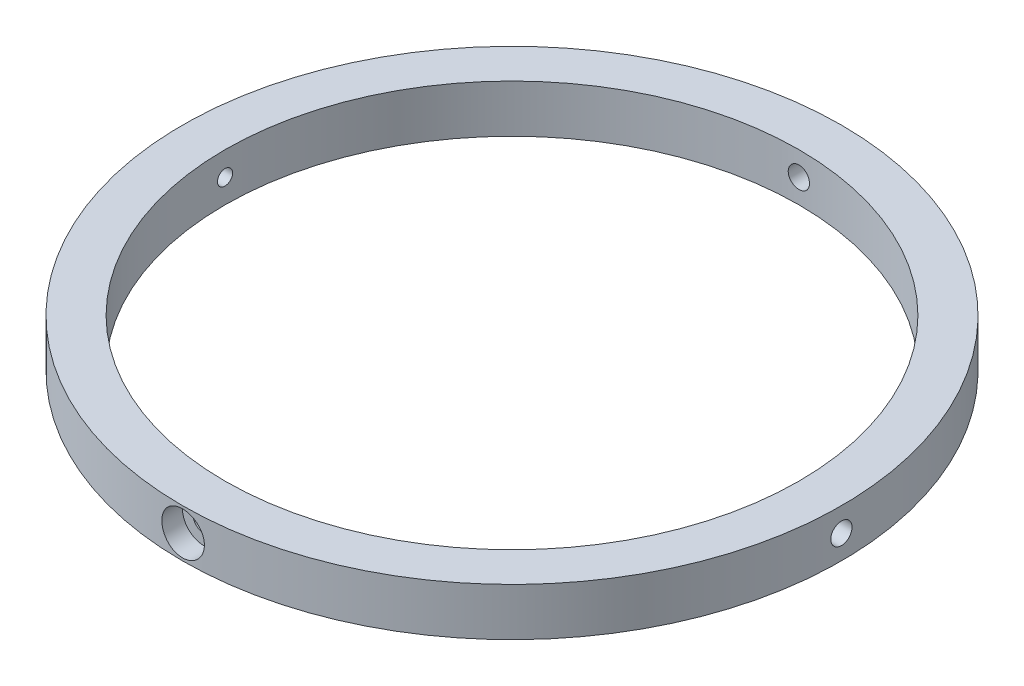
SolidWorks part; units mm, degrees
material "6061-T6 (SS)"
ref_plane "Front Plane" through (0, 0, 0) normal (0, 0, 1) x (1, 0, 0)
ref_plane "Top Plane" through (0, 0, 0) normal (0, 1, 0) x (1, 0, 0)
ref_plane "Right Plane" through (0, 0, 0) normal (1, 0, 0) x (0, 0, -1)
sketch "Sketch1" plane through (0, 0, 0) normal (0, 1, 0) x (1, 0, 0)
  circle A0 centre (0, 0) radius 49.2125
  circle A1 centre (0, 0) radius 42.8625
  dimension "D1" = 98.425
  dimension "D2" = 6.35
extrude "Boss-Extrude1" add sketch "Sketch1" along normal mid plane 7.1437
hole_wizard "Hole2" positions "3DSketch1" profile "Sketch3" legacy
sketch3d "3DSketch1"
  point P0 (49.2125, 0, 0)
  point P3 (0, 0, 0)
sketch "Sketch3" plane through (49.2125, 0, 0) normal (0, 1, 0) x (0, 0, -1)
  line L0 (0, 0) -> (0, 2.3813)
  line L1 (0, 2.3813) -> (1.5875, 2.3813)
  line L2 (1.5875, 2.3813) -> (1.5875, 0)
  line L3 (1.5875, 0) -> (0, 0)
  line L4 (0, 110) -> (0, -10) construction
  dimension "Diameter" = 3.175
  dimension "Depth" = 2.3813
hole_wizard "#4-40 Tapped Hole1" positions "Sketch6" profile "Sketch7" tap size "#4-40" standard "ANSI Inch"
sketch "Sketch6" plane through (46.8313, 0, 0) normal (1, 0, 0) x (0, 0, -1)
  point P0 (0, 0)
cosmetic thread "Hole Thread1" parameters "D1"=3.9899, "D2"=2.8448
sketch "Sketch7" plane through (46.8313, 0, 0) normal (0, 1, 0) x (0, 0, -1)
  line L0 (0, 0) -> (0, 9.5692)
  line L1 (0, 9.5692) -> (1.1303, 8.89)
  line L2 (1.1303, 8.89) -> (1.1303, 0)
  line L5 (1.1303, 0) -> (0, 0)
  line L10 (0, 9.5692) -> (-1.1303, 8.89) construction
  line L11 (0, -6.35) -> (0, 107.95) construction
  dimension "Tap Drill Dia." = 2.2606
  dimension "Tap Drill Depth" = 8.89
  dimension "Drill Angle" = 118
hole_wizard "Hole1" positions "3DSketch2" profile "Sketch5" legacy
sketch3d "3DSketch2"
  point P0 (0, 0, -49.2125)
  point P3 (0, 0, 0)
sketch "Sketch5" plane through (0, 0, -49.2125) normal (1, 0, 0) x (0, 1, 0)
  line L0 (0, 0) -> (0, 12.7)
  line L1 (0, 12.7) -> (1.5875, 12.7)
  line L2 (1.5875, 12.7) -> (1.5875, 3.175)
  line L3 (1.5875, 3.175) -> (3.175, 3.175)
  line L4 (3.175, 3.175) -> (3.175, 0)
  line L5 (3.175, 0) -> (0, 0)
  line L6 (0, 110) -> (0, -10) construction
  dimension "Diameter" = 3.175
  dimension "Depth" = 12.7
  dimension "C-Bore Diameter" = 6.35
  dimension "C-Bore Depth" = 3.175
pattern_circular "CirPattern1" count 2 over 360 about axis through (0, 0, 0) along (0, 1, 0) of "Hole1", "Hole2", "#4-40 Tapped Hole1"
